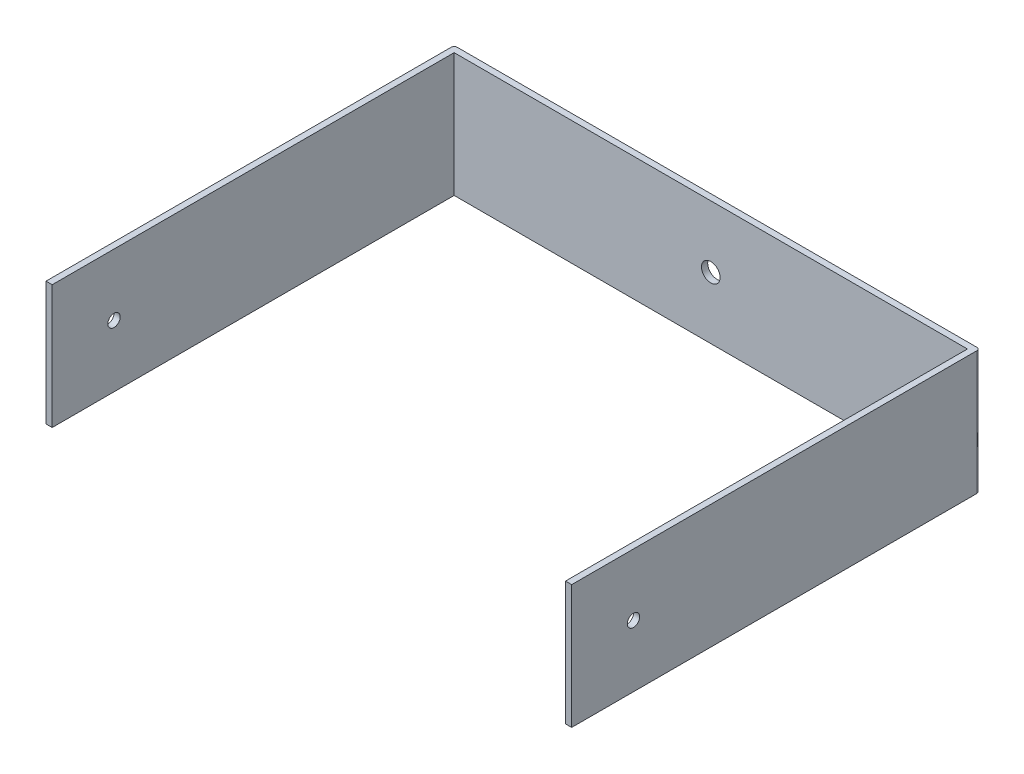
SolidWorks part; units mm, degrees
ref_plane "Plan de face" through (0, 0, 0) normal (0, 0, 1) x (1, 0, 0)
ref_plane "Plan de dessus" through (0, 0, 0) normal (0, 1, 0) x (1, 0, 0)
ref_plane "Plan de droite" through (0, 0, 0) normal (1, 0, 0) x (0, 0, -1)
sketch "Esquisse1" plane through (0, 0, 0) normal (0, 0, 1) x (1, 0, 0)
  line L1 (0, 0) -> (170, 0)
  line L2 (0, 0) -> (0, -40)
  line L3 (0, -40) -> (170, -40)
  line L4 (170, 0) -> (170, -40)
  dimension "D1" = 170
  dimension "D2" = 40
extrude "Boss.-Extru.1" add sketch "Esquisse1" along normal blind 2
sketch "Esquisse2" plane through (0, 0, 2) normal (0, 0, 1) x (1, 0, 0)
  line L0 (0, -40) -> (170, -40) construction
  line L1 (0, 0) -> (2, 0)
  line L2 (0, 0) -> (0, -40)
  line L3 (0, -40) -> (2, -40)
  line L4 (2, 0) -> (2, -40)
  dimension "D1" = 2
extrude "Boss.-Extru.2" add sketch "Esquisse2" along normal blind 130
sketch "Esquisse3" plane through (0, 0, 2) normal (0, 0, 1) x (1, 0, 0)
  line L0 (2, -40) -> (170, -40) construction
  line L1 (170, 0) -> (168, 0)
  line L2 (170, 0) -> (170, -40)
  line L3 (170, -40) -> (168, -40)
  line L4 (168, 0) -> (168, -40)
  dimension "D1" = 2
extrude "Boss.-Extru.3" add sketch "Esquisse3" along normal blind 130
sketch "Esquisse4" plane through (0, 0, 0) normal (-1, 0, 0) x (0, 0, 1)
  line L0 (132, 0) -> (132, -40) construction
  line L1 (132, -40) -> (0, -40) construction
  circle A0 centre (112, -20) radius 2
  dimension "D3" = 4
  dimension "D1" = 20
  dimension "D2" = 20
extrude "Enlèv. mat.-Extru.1" cut sketch "Esquisse4" against normal through all
fillet "Congé1" radius 1 1 edges at (0, -20, 0)
fillet "Congé2" radius 1 1 edges at (170, -20, 0)
sketch "Esquisse5" plane through (0, 0, 2) normal (0, 0, 1) x (1, 0, 0)
  line L0 (168, 0) -> (2, 0) construction
  line L1 (170, -40) -> (170, 0) construction
  circle A0 centre (85, -20) radius 3
  dimension "D2" = 6
  dimension "D1" = 20
  dimension "D3" = 85
extrude "Enlèv. mat.-Extru.2" cut sketch "Esquisse5" against normal blind 130
